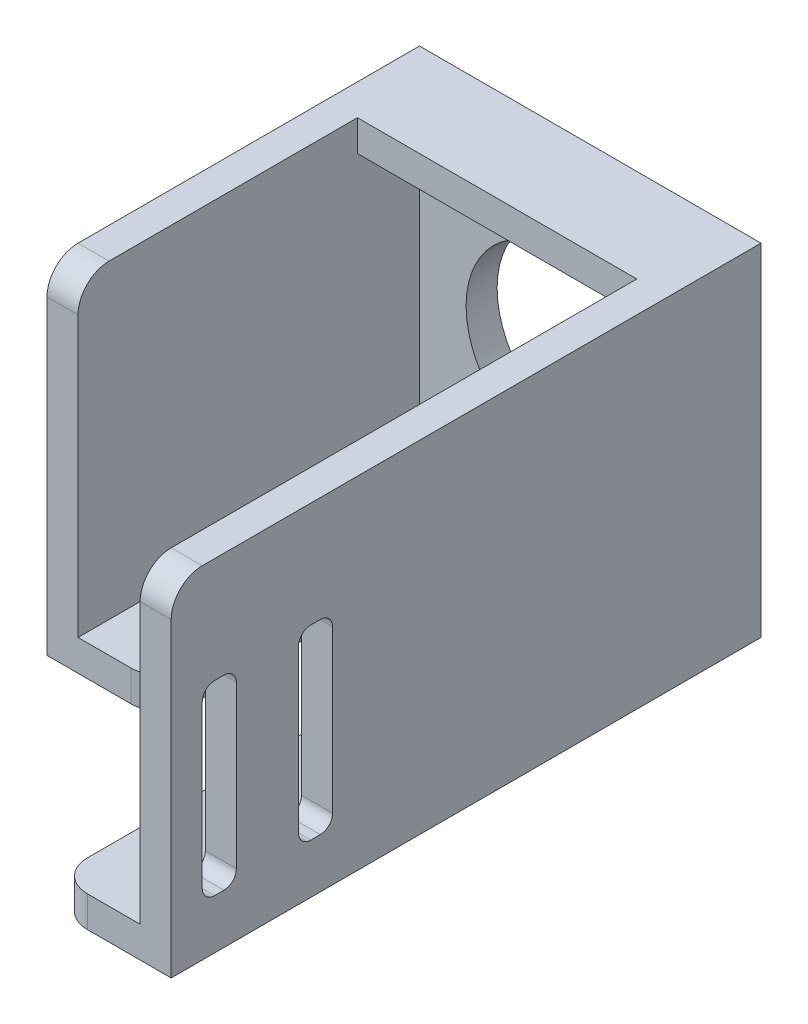
SolidWorks part; units mm, degrees
ref_plane "Alzado" through (0, 0, 0) normal (0, 0, 1) x (1, 0, 0)
ref_plane "Planta" through (0, 0, 0) normal (0, 1, 0) x (1, 0, 0)
ref_plane "Vista lateral" through (0, 0, 0) normal (1, 0, 0) x (0, 0, -1)
sketch "Croquis1" plane through (0, 0, 0) normal (0, 0, 1) x (1, 0, 0)
  line L1 (0, 0) -> (55, 0)
  line L2 (0, 0) -> (0, -55)
  line L3 (0, -55) -> (55, -55)
  line L4 (55, 0) -> (55, -55)
  point P4 (0, 0)
  point P6 (0, 0)
  dimension "D1" = 55
  dimension "D2" = 55
extrude "Saliente-Extruir1" add sketch "Croquis1" along normal blind 60
sketch "Croquis2" plane through (0, 0, 60) normal (0, 0, 1) x (1, 0, 0)
  line L0 (0, 0) -> (0, -55) construction
  line L1 (5, -5) -> (50, -5)
  line L2 (5, -5) -> (5, -50)
  line L3 (5, -50) -> (50, -50)
  line L4 (50, -5) -> (50, -50)
  line L5 (55, 0) -> (0, 0) construction
  line L6 (55, -55) -> (55, 0) construction
  line L7 (0, -55) -> (55, -55) construction
  dimension "D1" = 5
  dimension "D2" = 5
  dimension "D3" = 5
  dimension "D4" = 5
extrude "Cortar-Extruir1" cut sketch "Croquis2" against normal blind 55
sketch "Croquis3" plane through (0, -55, 0) normal (0, -1, 0) x (1, 0, 0)
  line L0 (0, 60) -> (55, 60) construction
  line L5 (18.5, 60) -> (36.5, 60)
  line L6 (18.5, 60) -> (18.5, 20)
  line L7 (18.5, 20) -> (36.5, 20)
  line L8 (36.5, 60) -> (36.5, 20)
  line L9 (0, 0) -> (55, 0) construction
  point P8 (27.5, 60)
  point P9 (27.5, 0)
  dimension "D1" = 20
  dimension "D2" = 18
  dimension "D3" = 0
extrude "Cortar-Extruir2" cut sketch "Croquis3" against normal up to next
sketch "Croquis4" plane through (0, 0, 0) normal (0, 1, 0) x (1, 0, 0)
  line L0 (55, -60) -> (0, -60) construction
  line L1 (5, -60) -> (50, -60)
  line L2 (5, -60) -> (5, -15)
  line L3 (5, -15) -> (50, -15)
  line L4 (50, -60) -> (50, -15)
  line L5 (0, -60) -> (0, 0) construction
  line L6 (55, -60) -> (55, 0) construction
  line L7 (55, 0) -> (0, 0) construction
  dimension "D1" = 5
  dimension "D2" = 5
  dimension "D3" = 15
extrude "Cortar-Extruir3" cut sketch "Croquis4" against normal up to next
sketch "Croquis5" plane through (0, 0, 0) normal (0, 0, -1) x (-1, 0, 0)
  line L0 (-55, 0) -> (0, -55) construction
  line L1 (0, 0) -> (-55, -55) construction
  line L3 (-45, -10) -> (-10, -10) construction
  line L4 (-45, -10) -> (-45, -45) construction
  line L5 (-45, -45) -> (-10, -45) construction
  line L6 (-10, -10) -> (-10, -45) construction
  line L7 (-45, -10) -> (-10, -45) construction
  line L8 (-45, -45) -> (-10, -10) construction
  circle A0 centre (-45, -10) radius 1.5
  circle A1 centre (-10, -10) radius 1.5
  circle A2 centre (-45, -45) radius 1.5
  circle A3 centre (-10, -45) radius 1.5
  circle A4 centre (-27.5, -27.5) radius 15
  point P8 (-27.5, -27.5)
  dimension "D3" = 3
  dimension "D4" = 3
  dimension "D5" = 3
  dimension "D6" = 3
  dimension "D7" = 30
  dimension "D1" = 35
  dimension "D2" = 35
extrude "Cortar-Extruir4" cut sketch "Croquis5" against normal up to next
sketch "Croquis6" plane through (0, 0, 60) normal (0, 0, 1) x (1, 0, 0)
  line L0 (50, 0) -> (55, 0)
  line L1 (55, 0) -> (55, -55)
  line L2 (55, -55) -> (36.5, -55)
  line L3 (36.5, -55) -> (36.5, -50)
  line L4 (36.5, -50) -> (50, -50)
  line L5 (50, -50) -> (50, 0)
extrude "Saliente-Extruir2" add sketch "Croquis6" along normal blind 35
fillet "Redondeo3" radius 5 6 edges at (36.5, -52.5, 20) (18.5, -52.5, 20) (36.5, -52.5, 95) (52.5, 0, 95) (2.5, 0, 60) (18.5, -52.5, 60)
sketch "Croquis7" plane through (50, 0, 0) normal (-1, 0, 0) x (0, 0, 1)
  line L0 (95, -5) -> (95, -50) construction
  line L1 (84.5, -17) -> (90, -17)
  line L2 (84.5, -17) -> (84.5, -47)
  line L3 (84.5, -47) -> (90, -47)
  line L4 (90, -17) -> (90, -47)
  line L5 (69, -17) -> (74.5, -17)
  line L6 (69, -17) -> (69, -47)
  line L7 (69, -47) -> (74.5, -47)
  line L8 (74.5, -17) -> (74.5, -47)
  line L9 (5, -50) -> (95, -50) construction
  dimension "D1" = 5.5
  dimension "D2" = 5.5
  dimension "D3" = 10
  dimension "D4" = 5
  dimension "D5" = 3
  dimension "D6" = 3
  dimension "D7" = 30
  dimension "D8" = 30
extrude "Cortar-Extruir5" cut sketch "Croquis7" against normal up to next
fillet "Redondeo4" radius 2 8 edges at (52.5, -47, 69) (52.5, -47, 84.5) (52.5, -47, 74.5) (52.5, -47, 90) (52.5, -17, 69) (52.5, -17, 84.5) (52.5, -17, 74.5) (52.5, -17, 90)
